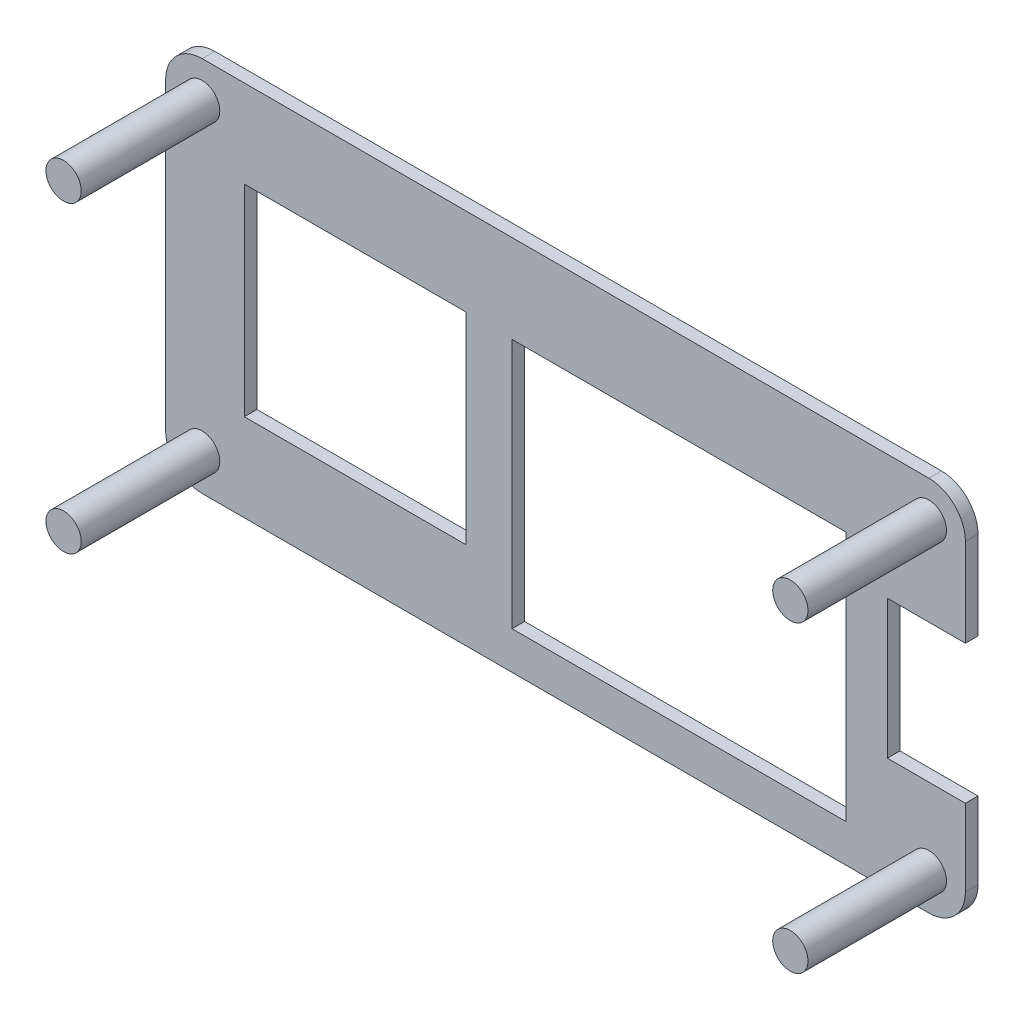
SolidWorks part; units mm, degrees
ref_plane "前视基准面" through (0, 0, 0) normal (0, 0, 1) x (1, 0, 0)
ref_plane "上视基准面" through (0, 0, 0) normal (0, 1, 0) x (1, 0, 0)
ref_plane "右视基准面" through (0, 0, 0) normal (1, 0, 0) x (0, 0, -1)
sketch "草图1" plane through (0, 0, 0) normal (0, 0, 1) x (1, 0, 0)
  line L13 (0, -2.9) -> (57.7, -2.9)
  line L21 (0, 27) -> (57.7, 27)
  line L22 (-2.9, 0) -> (-2.9, 24.1)
  line L23 (60.6, 0) -> (60.6, 24.1)
  arc A25 (0, -2.9) -> (-2.9, 0) centre (0, 0) cw
  arc A26 (0, 27) -> (-2.9, 24.1) centre (0, 24.1) ccw
  arc A27 (60.6, 24.1) -> (57.7, 27) centre (57.7, 24.1) ccw
  arc A28 (57.7, -2.9) -> (60.6, 0) centre (57.7, 0) ccw
extrude "凸台-拉伸1" add sketch "草图1" along normal blind 1 contours L21 A27 L23 A28 L13 A25 L22 A26
sketch "草图2" plane through (0, 0, 0) normal (0, 0, 1) x (1, 0, 0)
  circle A29 centre (0, 24.1) radius 1.4
  circle A31 centre (0, 0) radius 1.4
  circle A32 centre (57.7, 0) radius 1.4
  circle A33 centre (57.7, 24.1) radius 1.4
extrude "凸台-拉伸2" add sketch "草图2" along normal blind 12
sketch "草图10" plane through (0, 0, 1) normal (0, 0, 1) x (1, 0, 0)
  line L0 (20.95, 4.05) -> (20.95, 20.05)
  line L4 (60.6, 0) -> (60.6, 24.1) construction
  line L5 (3.35, 4.05) -> (3.35, 20.05)
  line L6 (0, -2.9) -> (57.7, -2.9) construction
  line L7 (3.35, 4.05) -> (20.95, 4.05)
  line L8 (3.35, 20.05) -> (20.95, 20.05)
  line L9 (0, 27) -> (57.7, 27) construction
  line L10 (60.6, 17.1) -> (60.6, 6.1)
  line L12 (54.4, 6.1) -> (60.6, 6.1)
  line L13 (60.6, 0) -> (60.6, 24.1) construction
  line L14 (51.1, 20) -> (24.6, 20)
  line L15 (51.1, 20) -> (51.1, 0.1)
  line L16 (51.1, 0.1) -> (24.6, 0.1)
  line L17 (24.6, 20) -> (24.6, 0.1)
  line L18 (54.4, 6.1) -> (54.4, 17.1)
  line L19 (54.4, 17.1) -> (60.6, 17.1)
  dimension "D1" = 26.5
  dimension "D2" = 9.5
  dimension "D3" = 3
  dimension "D4" = 3.65
  dimension "D5" = 17.6
  dimension "D6" = 7
  dimension "D7" = 6.95
  dimension "D8" = 6.95
extrude "切除-拉伸1" cut sketch "草图10" against normal through all
